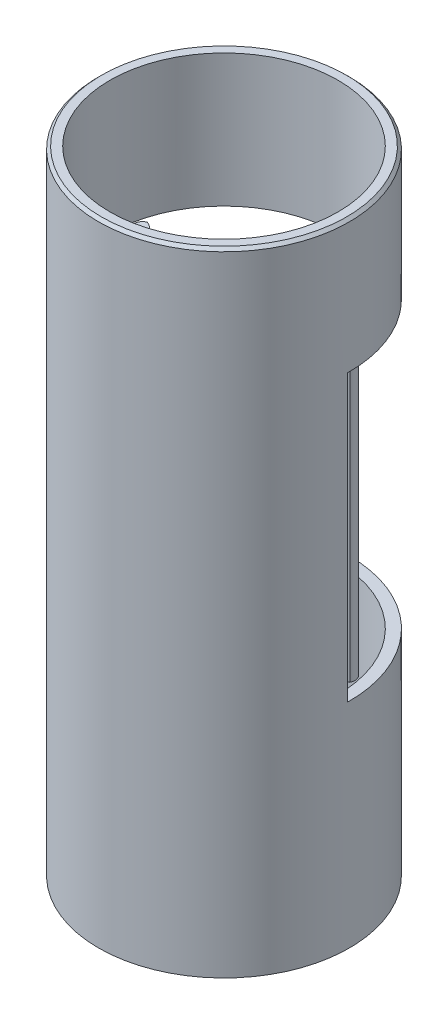
SolidWorks part; units mm, degrees
ref_plane "Front Plane" through (0, 0, 0) normal (0, 0, 1) x (1, 0, 0)
ref_plane "Top Plane" through (0, 0, 0) normal (0, 1, 0) x (1, 0, 0)
ref_plane "Right Plane" through (0, 0, 0) normal (1, 0, 0) x (0, 0, -1)
sketch "Sketch1" plane through (0, 0, 0) normal (0, 1, 0) x (1, 0, 0)
  circle A0 centre (0, 0) radius 17.6
  circle A1 centre (0, 0) radius 16
  dimension "D1" = 35.2
  dimension "D2" = 32
extrude "Boss-Extrude1" add sketch "Sketch1" along normal blind 18.6
sketch "Sketch2" plane through (0, 0, 0) normal (0, -1, 0) x (1, 0, 0)
  line L0 (-17.5974, 0.3) -> (17.5974, 0.3) construction
  line L1 (-17.5974, 0.3) -> (-15.9972, 0.3)
  line L2 (17.5974, 0.3) -> (15.9972, 0.3)
  arc A0 (-17.5974, 0.3) -> (17.5974, 0.3) centre (0, 0) cw
  arc A1 (15.3586, -2.3) -> (14.7284, -3.9861) centre (14.3, -2.8652) cw
  circle A2 centre (0, 0) radius 17.6 construction
  circle A3 centre (0, 0) radius 16 construction
  arc A6 (-15.9972, 0.3) -> (-15.3586, -2.3) centre (-15.9642, -1.0703) cw
  arc A7 (15.9972, 0.3) -> (15.3586, -2.3) centre (15.9642, -1.0703) ccw
  arc A8 (-14.7284, -3.9861) -> (-15.8623, 2.0949) centre (-15.9642, -1.0703) ccw
  arc A9 (-15.3586, -2.3) -> (-14.7284, -3.9861) centre (-14.3, -2.8652) ccw
  arc A10 (14.7284, -3.9861) -> (15.8623, 2.0949) centre (15.9642, -1.0703) cw
  arc A11 (-15.8623, 2.0949) -> (15.8623, 2.0949) centre (0, 0) cw
  dimension "D5" = 1.2
  dimension "D1" = 0.3
  dimension "D2" = 2.6
  dimension "D3" = 1.8
  dimension "D4" = 1.7949
  dimension "D6" = 28.6
extrude "Boss-Extrude4" add sketch "Sketch2" along normal blind 40
fillet "Fillet1" radius 3 2 edges at (-15.8623, -20, 2.0949) (15.8623, -20, 2.0949)
sketch "Sketch3" plane through (0, -40, 0) normal (0, -1, 0) x (1, 0, 0)
  circle A0 centre (0, 0) radius 16
  circle A1 centre (0, 0) radius 17.6
  circle A2 centre (0, 0) radius 16 construction
  circle A3 centre (0, 0) radius 17.6 construction
extrude "Boss-Extrude5" add sketch "Sketch3" along normal blind 30
chamfer "Chamfer1" distance 0.4 angle 45 1 edges at (0, 18.6, 17.6)
